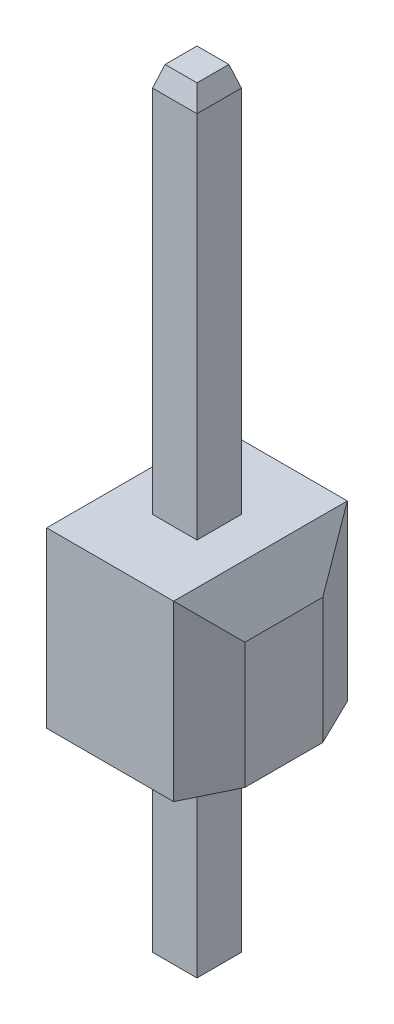
SolidWorks part; units mm, degrees
ref_plane "Front Plane" through (0, 0, 0) normal (0, 0, 1) x (1, 0, 0)
ref_plane "Top Plane" through (0, 0, 0) normal (0, 1, 0) x (1, 0, 0)
ref_plane "Right Plane" through (0, 0, 0) normal (1, 0, 0) x (0, 0, -1)
sketch "Sketch1" plane through (0, 0, 0) normal (0, 1, 0) x (1, 0, 0)
  line L1 (-1.27, -1.27) -> (1.27, -1.27)
  line L2 (-1.27, -1.27) -> (-1.27, 1.27)
  line L3 (-1.27, 1.27) -> (1.27, 1.27)
  line L4 (1.27, -1.27) -> (1.27, 1.27)
  line L5 (-1.27, -1.27) -> (1.27, 1.27) construction
  line L6 (-1.27, 1.27) -> (1.27, -1.27) construction
  point P0 (0, 0)
  dimension "D1" = 2.54
  dimension "D2" = 2.54
extrude "Boss-Extrude1" add sketch "Sketch1" along normal blind 2.54
sketch "Sketch2" plane through (0, 2.54, 0) normal (0, 1, 0) x (1, 0, 0)
  line L1 (0.325, -0.325) -> (-0.325, -0.325)
  line L2 (0.325, -0.325) -> (0.325, 0.325)
  line L3 (0.325, 0.325) -> (-0.325, 0.325)
  line L4 (-0.325, -0.325) -> (-0.325, 0.325)
  line L5 (0.325, -0.325) -> (-0.325, 0.325) construction
  line L6 (0.325, 0.325) -> (-0.325, -0.325) construction
  point P0 (0, 0)
  dimension "D1" = 0.65
  dimension "D2" = 0.65
extrude "Boss-Extrude2" add sketch "Sketch2" along normal blind 5.7 and the other way blind 5.64
chamfer "Chamfer1" distance 0.3 angle 17 8 edges at (0.325, -3.1, 0) (0, -3.1, -0.325) (0, -3.1, 0.325) (-0.325, -3.1, 0) (0, 8.24, -0.325) (-0.325, 8.24, 0) (0, 8.24, 0.325) (0.325, 8.24, 0)
chamfer "Chamfer3" distance 0.7 angle 26 3 edges at (1.27, 1.27, -1.27) (1.27, 1.27, 1.27) (1.27, 2.54, 0)
chamfer "Chamfer4" distance 0.7 angle 26 3 edges at (-1.27, 1.27, -1.27) (-1.27, 1.27, 1.27) (-1.27, 2.54, 0)
